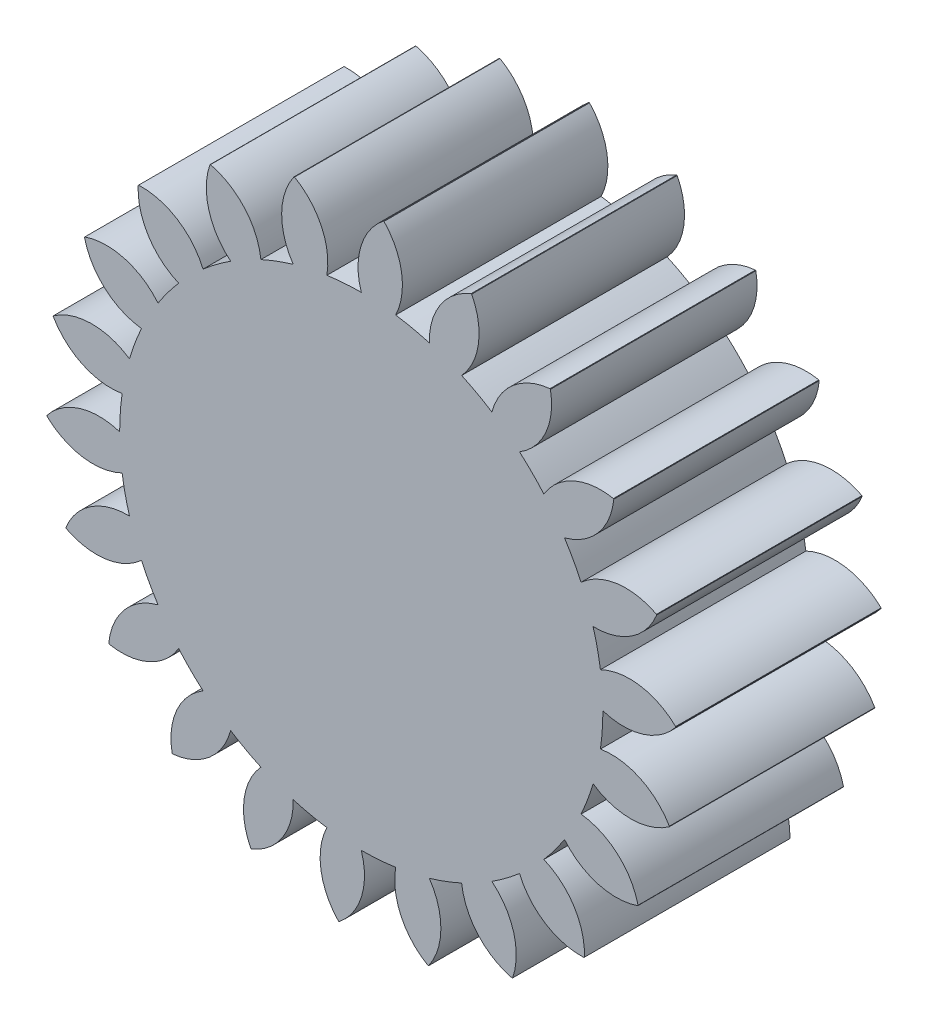
SolidWorks part; units mm, degrees
ref_plane "Front Plane" through (0, 0, 0) normal (0, 0, 1) x (1, 0, 0)
ref_plane "Top Plane" through (0, 0, 0) normal (0, 1, 0) x (1, 0, 0)
ref_plane "Right Plane" through (0, 0, 0) normal (1, 0, 0) x (0, 0, -1)
sketch "Sketch1" plane through (0, 0, 0) normal (0, 0, 1) x (1, 0, 0)
  line L0 (1.7677, 4.8566) -> (0, 0) construction
  line L1 (0, 0) -> (-0.5145, 7.1932) construction
  line L2 (-0.7827, 5.444) -> (0, 0)
  line L3 (0, 0) -> (3.0865, 4.1455)
  line L4 (3.0865, 4.1455) -> (0.4322, 6.1217)
  line L5 (0.4322, 6.1217) -> (0, 0)
  line L6 (0, 4.7038) -> (0, 0) construction
  line L7 (0, 5.5) -> (1.7677, 4.8566)
  circle A0 centre (0, 0) radius 5.5 construction
  circle A1 centre (0, 0) radius 5.1683
  circle A2 centre (0, 0) radius 6.1369
  circle A3 centre (0, 0) radius 4.7038
  circle A4 centre (1.2359, 5.1019) radius 1.2984
  circle A5 centre (-1.9494, 4.8741) radius 1.2984
  point P11 (-0.7827, 5.444)
  point P16 (-3.1872, 4.4824)
  dimension "D1" = 11
  dimension "D2" = 10.3366
  dimension "D3" = 12.2739
  dimension "D4" = 9.4076
  dimension "D5" = 36.669
  dimension "D6" = 20
  dimension "D7" = 8.182
extrude "Boss-Extrude1" add sketch "Sketch1" along normal blind 4 contours A5 A3 L2 A1 | A3 A5 A1 L3 | A3 A4 A1 L5 | A4 A3 L3 A1 | A1 A4 A3 L5 | A5 A1 L2 | A5 A1 L2 A2 | A5 L2 A1 | L7 A4 A1 L5 | L5 A4 L7 | A1 A4 L4 L5 L7 | A1 L7 L5 | L4 A4 A2 | A1 A5 A2 A4 L4 | A4 A1 L4
sketch "Sketch2" plane through (0, 0, 4) normal (0, 0, 1) x (1, 0, 0)
  line L0 (-1.964, 6.1724) -> (1.0656, 6.3891)
  line L1 (-0.1454, 6.4757) -> (2.8224, 5.8301)
  line L2 (1.6849, 6.2544) -> (4.3506, 4.7988)
  line L3 (3.3787, 5.5263) -> (5.5263, 3.3787)
  line L4 (4.7988, 4.3506) -> (6.2544, 1.6849)
  line L5 (5.8301, 2.8224) -> (6.4757, -0.1454)
  line L6 (6.3891, 1.0656) -> (6.1724, -1.964)
  line L7 (6.4305, -0.7776) -> (5.3691, -3.6234)
  line L8 (5.9509, -2.5578) -> (4.1308, -4.9893)
  line L9 (4.9893, -4.1308) -> (2.5578, -5.9509)
  line L10 (3.6234, -5.3691) -> (0.7776, -6.4305)
  line L11 (1.964, -6.1724) -> (-1.0656, -6.3891)
  line L12 (0.1454, -6.4757) -> (-2.8224, -5.8301)
  line L13 (-1.6849, -6.2544) -> (-4.3506, -4.7988)
  line L14 (-3.3787, -5.5263) -> (-5.5263, -3.3787)
  line L15 (-4.7988, -4.3506) -> (-6.2544, -1.6849)
  line L16 (-5.8301, -2.8224) -> (-6.4757, 0.1454)
  line L17 (-6.3891, -1.0656) -> (-6.1724, 1.964)
  line L18 (-6.4305, 0.7776) -> (-5.3691, 3.6234)
  line L19 (-5.9509, 2.5578) -> (-4.1308, 4.9893)
  line L20 (-4.9893, 4.1308) -> (-2.5578, 5.9509)
  line L21 (-3.6234, 5.3691) -> (-0.7776, 6.4305)
  arc A0 (0.4322, 6.1217) -> (0, 4.7038) centre (1.2359, 5.1019) ccw construction
  arc A1 (0, 4.7038) -> (-0.6694, 4.6559) centre (0, 0) ccw construction
  arc A2 (-0.6694, 4.6559) -> (-1.299, 5.9979) centre (-1.9494, 4.8741) ccw construction
  arc A3 (1.0656, 6.3891) -> (0, 4.7038) centre (1.2359, 5.1019) ccw
  arc A4 (0, 4.7038) -> (-0.6694, 4.6559) centre (0, 0) ccw
  arc A5 (-0.6694, 4.6559) -> (-1.964, 6.1724) centre (-1.9494, 4.8741) ccw
  arc A6 (2.8224, 5.8301) -> (1.3252, 4.5133) centre (2.6232, 4.5471) ccw
  arc A7 (1.3252, 4.5133) -> (0.6694, 4.6559) centre (0, 0) ccw
  arc A8 (0.6694, 4.6559) -> (-0.1454, 6.4757) centre (-0.4972, 5.2259) ccw
  arc A9 (4.3506, 4.7988) -> (2.5431, 3.9571) centre (3.798, 3.6238) ccw
  arc A10 (2.5431, 3.9571) -> (1.954, 4.2787) centre (0, 0) ccw
  arc A11 (1.954, 4.2787) -> (1.6849, 6.2544) centre (0.9952, 5.1543) ccw
  arc A12 (5.5263, 3.3787) -> (3.5549, 3.0803) centre (4.6651, 2.407) ccw
  arc A13 (3.5549, 3.0803) -> (3.0803, 3.5549) centre (0, 0) ccw
  arc A14 (3.0803, 3.5549) -> (3.3787, 5.5263) centre (2.407, 4.6651) ccw
  arc A15 (6.2544, 1.6849) -> (4.2787, 1.954) centre (5.1543, 0.9952) ccw
  arc A16 (4.2787, 1.954) -> (3.9571, 2.5431) centre (0, 0) ccw
  arc A17 (3.9571, 2.5431) -> (4.7988, 4.3506) centre (3.6238, 3.798) ccw
  arc A18 (6.4757, -0.1454) -> (4.6559, 0.6694) centre (5.2259, -0.4972) ccw
  arc A19 (4.6559, 0.6694) -> (4.5133, 1.3252) centre (0, 0) ccw
  arc A20 (4.5133, 1.3252) -> (5.8301, 2.8224) centre (4.5471, 2.6232) ccw
  arc A21 (6.1724, -1.964) -> (4.6559, -0.6694) centre (4.8741, -1.9494) ccw
  arc A22 (4.6559, -0.6694) -> (4.7038, 0) centre (0, 0) ccw
  arc A23 (4.7038, 0) -> (6.3891, 1.0656) centre (5.1019, 1.2359) ccw
  arc A24 (5.3691, -3.6234) -> (4.2787, -1.954) centre (4.1275, -3.2436) ccw
  arc A25 (4.2787, -1.954) -> (4.5133, -1.3252) centre (0, 0) ccw
  arc A26 (4.5133, -1.3252) -> (6.4305, -0.7776) centre (5.2434, -0.2516) ccw
  arc A27 (4.1308, -4.9893) -> (3.5549, -3.0803) centre (3.0465, -4.275) ccw
  arc A28 (3.5549, -3.0803) -> (3.9571, -2.5431) centre (0, 0) ccw
  arc A29 (3.9571, -2.5431) -> (5.9509, -2.5578) centre (4.9602, -1.7186) ccw
  arc A30 (2.5578, -5.9509) -> (2.5431, -3.9571) centre (1.7186, -4.9602) ccw
  arc A31 (2.5431, -3.9571) -> (3.0803, -3.5549) centre (0, 0) ccw
  arc A32 (3.0803, -3.5549) -> (4.9893, -4.1308) centre (4.275, -3.0465) ccw
  arc A33 (0.7776, -6.4305) -> (1.3252, -4.5133) centre (0.2516, -5.2434) ccw
  arc A34 (1.3252, -4.5133) -> (1.954, -4.2787) centre (0, 0) ccw
  arc A35 (1.954, -4.2787) -> (3.6234, -5.3691) centre (3.2436, -4.1275) ccw
  arc A36 (-1.0656, -6.3891) -> (0, -4.7038) centre (-1.2359, -5.1019) ccw
  arc A37 (0, -4.7038) -> (0.6694, -4.6559) centre (0, 0) ccw
  arc A38 (0.6694, -4.6559) -> (1.964, -6.1724) centre (1.9494, -4.8741) ccw
  arc A39 (-2.8224, -5.8301) -> (-1.3252, -4.5133) centre (-2.6232, -4.5471) ccw
  arc A40 (-1.3252, -4.5133) -> (-0.6694, -4.6559) centre (0, 0) ccw
  arc A41 (-0.6694, -4.6559) -> (0.1454, -6.4757) centre (0.4972, -5.2259) ccw
  arc A42 (-4.3506, -4.7988) -> (-2.5431, -3.9571) centre (-3.798, -3.6238) ccw
  arc A43 (-2.5431, -3.9571) -> (-1.954, -4.2787) centre (0, 0) ccw
  arc A44 (-1.954, -4.2787) -> (-1.6849, -6.2544) centre (-0.9952, -5.1543) ccw
  arc A45 (-5.5263, -3.3787) -> (-3.5549, -3.0803) centre (-4.6651, -2.407) ccw
  arc A46 (-3.5549, -3.0803) -> (-3.0803, -3.5549) centre (0, 0) ccw
  arc A47 (-3.0803, -3.5549) -> (-3.3787, -5.5263) centre (-2.407, -4.6651) ccw
  arc A48 (-6.2544, -1.6849) -> (-4.2787, -1.954) centre (-5.1543, -0.9952) ccw
  arc A49 (-4.2787, -1.954) -> (-3.9571, -2.5431) centre (0, 0) ccw
  arc A50 (-3.9571, -2.5431) -> (-4.7988, -4.3506) centre (-3.6238, -3.798) ccw
  arc A51 (-6.4757, 0.1454) -> (-4.6559, -0.6694) centre (-5.2259, 0.4972) ccw
  arc A52 (-4.6559, -0.6694) -> (-4.5133, -1.3252) centre (0, 0) ccw
  arc A53 (-4.5133, -1.3252) -> (-5.8301, -2.8224) centre (-4.5471, -2.6232) ccw
  arc A54 (-6.1724, 1.964) -> (-4.6559, 0.6694) centre (-4.8741, 1.9494) ccw
  arc A55 (-4.6559, 0.6694) -> (-4.7038, 0) centre (0, 0) ccw
  arc A56 (-4.7038, 0) -> (-6.3891, -1.0656) centre (-5.1019, -1.2359) ccw
  arc A57 (-5.3691, 3.6234) -> (-4.2787, 1.954) centre (-4.1275, 3.2436) ccw
  arc A58 (-4.2787, 1.954) -> (-4.5133, 1.3252) centre (0, 0) ccw
  arc A59 (-4.5133, 1.3252) -> (-6.4305, 0.7776) centre (-5.2434, 0.2516) ccw
  arc A60 (-4.1308, 4.9893) -> (-3.5549, 3.0803) centre (-3.0465, 4.275) ccw
  arc A61 (-3.5549, 3.0803) -> (-3.9571, 2.5431) centre (0, 0) ccw
  arc A62 (-3.9571, 2.5431) -> (-5.9509, 2.5578) centre (-4.9602, 1.7186) ccw
  arc A63 (-2.5578, 5.9509) -> (-2.5431, 3.9571) centre (-1.7186, 4.9602) ccw
  arc A64 (-2.5431, 3.9571) -> (-3.0803, 3.5549) centre (0, 0) ccw
  arc A65 (-3.0803, 3.5549) -> (-4.9893, 4.1308) centre (-4.275, 3.0465) ccw
  arc A66 (-0.7776, 6.4305) -> (-1.3252, 4.5133) centre (-0.2516, 5.2434) ccw
  arc A67 (-1.3252, 4.5133) -> (-1.954, 4.2787) centre (0, 0) ccw
  arc A68 (-1.954, 4.2787) -> (-3.6234, 5.3691) centre (-3.2436, 4.1275) ccw
  point P131 (0, 0)
  point P136 (0, 0)
  arc M85 (-1.299, 5.9979) -> (0.4322, 6.1217) centre (0, 0) ccw
  dimension "D1" = 22
extrude "Cut-Extrude1" cut sketch "Sketch2" against normal blind 10 contours A62 A61 A60 M85 | A65 A64 A63 M85 | A68 A67 A66 M85 | A8 A7 A6 M85 | A11 A10 A9 M85 | A14 A13 A12 M85 | A17 A16 A15 M85 | A20 A19 A18 M85 | A23 A22 A21 M85 | A26 A25 A24 M85 | A29 A28 A27 M85 | A32 A31 A30 M85 | A35 A34 A33 M85 | A38 A37 A36 M85 | A41 A40 A39 M85 | A44 A43 A42 M85 | A47 A46 A45 M85 | A50 A49 A48 M85 | A53 A52 A51 M85 | A56 A55 A54 M85 | A59 A58 A57 M85
equation "\"module\"= 0.5mm"
equation "\"p\"= \"module\" * 3.14'Diametral pitch"
equation "\"n\"= 22'Number of teeth"
equation "\"phi\"= 20deg'Pressure angle"
equation "\"a\" = 1mm / \"p\"'Addendum"
equation "\"b\"= 1.25mm / \"p\"'Dedendum"
equation "\"c\"= \"b\" - \"a\"'Clearance"
equation "\"dp\"= \"module\" * \"n\"'Pitch circle diameter"
equation "\"db\"= \"dp\" * cos ( \"phi\" )'Base circle diameter"
equation "\"D1@Sketch1\"=\"dp\""
equation "\"D2@Sketch1\"=\"db\""
equation "\"D3@Sketch1\"=\"dp\"+ 2 * \"a\""
equation "\"D4@Sketch1\"=\"dp\"- 2 * \"b\""
equation "\"D6@Sketch1\"=\"phi\""
equation "\"D7@Sketch1\"=180 / \"n\""
